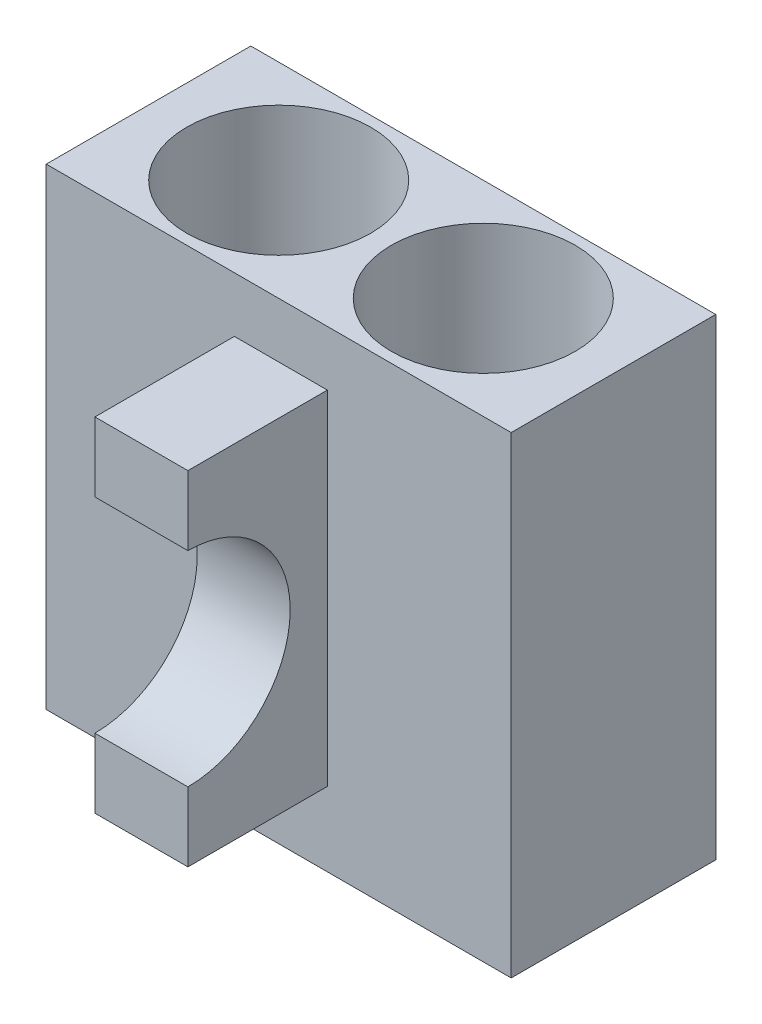
SolidWorks part; units mm, degrees
ref_plane "Front Plane" through (0, 0, 0) normal (0, 0, 1) x (1, 0, 0)
ref_plane "Top Plane" through (0, 0, 0) normal (0, 1, 0) x (1, 0, 0)
ref_plane "Right Plane" through (0, 0, 0) normal (1, 0, 0) x (0, 0, -1)
sketch "Sketch1" plane through (0, 0, 0) normal (0, 1, 0) x (1, 0, 0)
  line L1 (-20.0017, 10.7637) -> (29.9983, 10.7637)
  line L2 (-20.0017, 10.7637) -> (-20.0017, -11.2363)
  line L3 (-20.0017, -11.2363) -> (29.9983, -11.2363)
  line L4 (29.9983, 10.7637) -> (29.9983, -11.2363)
  circle A0 centre (-6.0017, -0.2363) radius 9.89
  circle A1 centre (15.9983, -0.2363) radius 9.89
  dimension "D1" = 19.78
  dimension "D2" = 19.78
  dimension "D3" = 11
  dimension "D4" = 16
  dimension "D5" = 22
  dimension "D6" = 11
  dimension "D7" = 50
  dimension "D8" = 14
  dimension "D9" = 14
extrude "Boss-Extrude1" add sketch "Sketch1" along normal blind 50.8
sketch "Sketch2" plane through (0, 0, 0) normal (0, 1, 0) x (1, 0, 0)
  circle A0 centre (15.9983, -0.2363) radius 10.5
  circle A1 centre (-6.0017, -0.2363) radius 10.5
  point P0 (-6.0017, -0.2363)
  point P1 (15.9983, -0.2363)
extrude "Boss-Extrude2" add sketch "Sketch2" along normal blind 1
sketch "Sketch3" plane through (0, 1, 0) normal (0, 1, 0) x (1, 0, 0)
  circle A0 centre (15.7037, 0) radius 10.5
extrude "Boss-Extrude3" add sketch "Sketch3" along normal blind 6.35
sketch "Sketch5" plane through (0, 0, 11.2363) normal (0, 0, 1) x (1, 0, 0)
  line L1 (0.2314, 44.8716) -> (10.2314, 44.8716)
  line L2 (0.2314, 44.8716) -> (0.2314, 7.9616)
  line L3 (0.2314, 7.9616) -> (10.2314, 7.9616)
  line L4 (10.2314, 44.8716) -> (10.2314, 7.9616)
  point P4 (5.2314, 26.4616)
  point P5 (0, 0)
  dimension "D1" = 36.91
  dimension "D2" = 10
  dimension "D3" = 5
  dimension "D4" = 18.5
extrude "Boss-Extrude4" add sketch "Sketch5" along normal blind 15
sketch "Sketch7" plane through (10.2314, 0, 0) normal (1, 0, 0) x (0, 0, -1)
  line L0 (-26.2363, 7.9616) -> (-26.2363, 44.8716) construction
  circle A0 centre (-26.2363, 26.4166) radius 11
  dimension "D1" = 22
extrude "Cut-Extrude1" cut sketch "Sketch7" against normal blind 10
